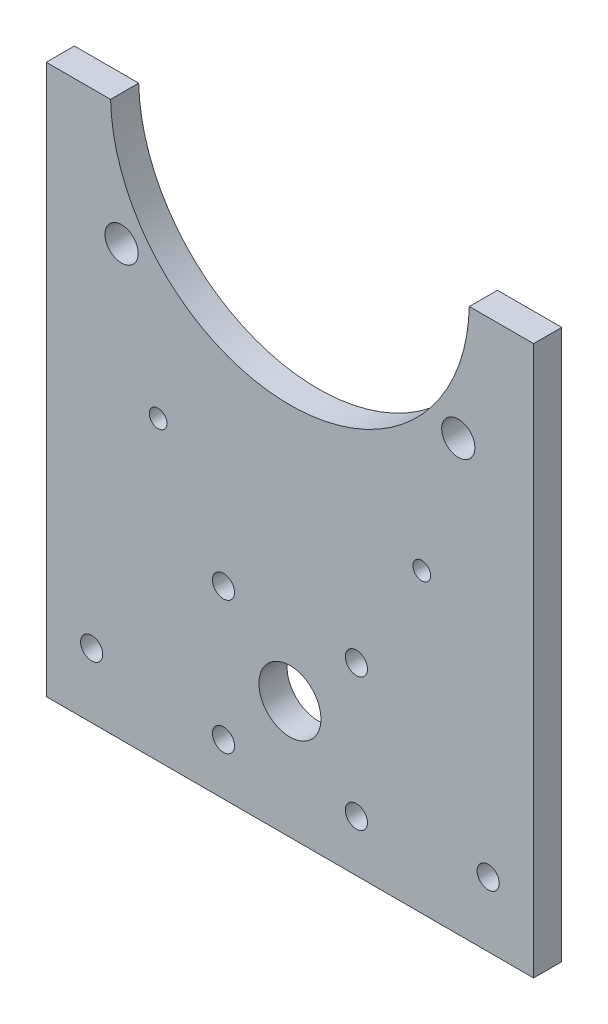
SolidWorks part; units mm, degrees
ref_plane "Alzado" through (0, 0, 0) normal (0, 0, 1) x (1, 0, 0)
ref_plane "Planta" through (0, 0, 0) normal (0, 1, 0) x (1, 0, 0)
ref_plane "Vista lateral" through (0, 0, 0) normal (1, 0, 0) x (0, 0, -1)
sketch "Croquis1" plane through (0, 0, 0) normal (0, 0, 1) x (1, 0, 0)
  line L0 (-110, 84.5) -> (0, 84.5) construction
  line L1 (0, 0) -> (-110, 0)
  line L2 (0, 0) -> (0, 124)
  line L4 (-110, 0) -> (-110, 124)
  line L5 (-110, 60) -> (0, 60) construction
  line L6 (-55, 0) -> (-55, 125) construction
  line L10 (-110, 50) -> (0, 50) construction
  line L11 (-110, 124) -> (-95.4877, 124)
  line L12 (0, 124) -> (-14.5123, 124)
  line L13 (-110, 14.601) -> (0, 14.601) construction
  line L16 (-99.75, 18.7706) -> (-99.75, 8.864) construction
  line L17 (-10.25, 18.7706) -> (-10.25, 8.864) construction
  circle A3 centre (-93, 97) radius 3.75
  circle A5 centre (-84.75, 67) radius 2
  arc A6 (-95.4877, 124) -> (-14.5123, 124) centre (-55, 125) ccw
  circle A7 centre (-25.25, 67) radius 2
  circle A8 centre (-17, 97) radius 3.75
  circle A11 centre (-99.75, 14.601) radius 2.5
  circle A12 centre (-10.25, 14.601) radius 2.5
  dimension "D4" = 76
  dimension "D7" = 59.5
  dimension "D8" = 7.5
  dimension "D9" = 4
  dimension "D10" = 7
  dimension "D11" = 10
  dimension "D1" = 110
  dimension "D2" = 124
  dimension "D3" = 39.5
  dimension "D5" = 24.5
  dimension "D6" = 37
  dimension "D12" = 50
extrude "Saliente-Extruir1" add sketch "Croquis1" along normal blind 6.35
sketch "Croquis2" plane through (0, 0, 6.35) normal (0, 0, 1) x (1, 0, 0)
  line L0 (-110, 26.601) -> (0, 26.601) construction
  line L1 (-110, 124) -> (-110, 0) construction
  line L2 (-70, 11.601) -> (-40, 11.601) construction
  line L3 (-70, 11.601) -> (-70, 41.601) construction
  line L4 (-70, 41.601) -> (-40, 41.601) construction
  line L5 (-40, 11.601) -> (-40, 41.601) construction
  line L6 (-70, 11.601) -> (-40, 41.601) construction
  line L7 (-70, 41.601) -> (-40, 11.601) construction
  line L8 (0, 0) -> (0, 124) construction
  circle A0 centre (-55, 26.601) radius 7
  circle A2 centre (-40, 11.601) radius 2.5
  circle A3 centre (-70, 11.601) radius 2.5
  circle A4 centre (-70, 41.601) radius 2.5
  circle A5 centre (-40, 41.601) radius 2.5
  dimension "D1" = 30
  dimension "D5" = 15
  dimension "D3" = 15
  dimension "D4" = 5
  dimension "D2" = 30
extrude "Cortar-Extruir1" cut sketch "Croquis2" against normal blind 10
